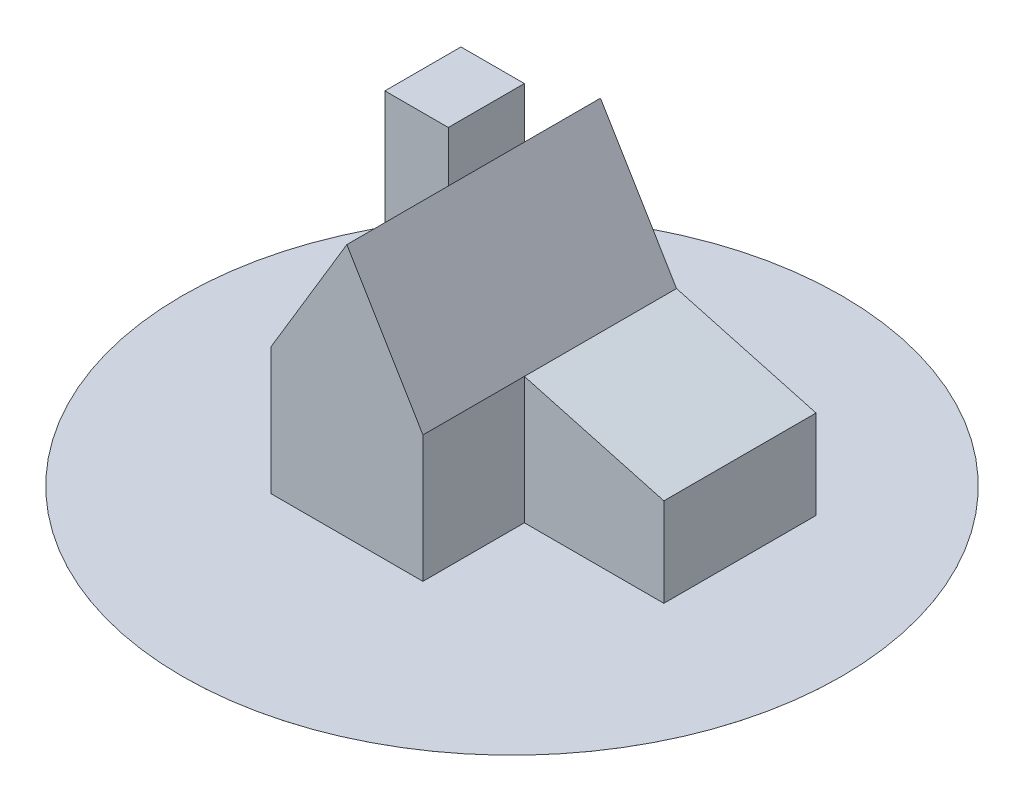
SolidWorks part; units mm, degrees
ref_plane "Front Plane" through (0, 0, 0) normal (0, 0, 1) x (1, 0, 0)
ref_plane "Top Plane" through (0, 0, 0) normal (0, 1, 0) x (1, 0, 0)
ref_plane "Right Plane" through (0, 0, 0) normal (1, 0, 0) x (0, 0, -1)
sketch "Sketch1" plane through (0, 0, 0) normal (0, 0, 1) x (1, 0, 0)
  line L0 (-60, 200) -> (0, 100)
  line L2 (-60, 200) -> (-120, 100)
  line L3 (-120, 100) -> (-120, 0)
  line L4 (-120, 0) -> (0, 0)
  line L5 (0, 100) -> (110, 70)
  line L6 (110, 70) -> (110, 0)
  line L7 (110, 0) -> (0, 0)
  dimension "D1" = 110
  dimension "D2" = 100
  dimension "D3" = 200
  dimension "D4" = 70
  dimension "D5" = 30
  dimension "D6" = 60
  dimension "D8" = 120
extrude "Extrude1" add sketch "Sketch1" along normal blind 200
sketch "Sketch2" plane through (0, 0, 0) normal (0, 1, 0) x (1, 0, 0)
  line L0 (0, -200) -> (0, 0) construction
  line L1 (110, -200) -> (0, -200)
  line L2 (110, -200) -> (110, -120)
  line L3 (110, -120) -> (0, -120)
  line L4 (0, -200) -> (0, -120)
  dimension "D1" = 80
extrude "Extrude2" cut sketch "Sketch2" along normal blind 200
sketch "Sketch3" plane through (0, 0, 0) normal (0, 1, 0) x (1, 0, 0)
  line L1 (-120, 0) -> (-170, 0)
  line L2 (-120, 0) -> (-120, -60)
  line L3 (-120, -60) -> (-170, -60)
  line L4 (-170, 0) -> (-170, -60)
  dimension "D1" = 50
  dimension "D2" = 60
extrude "Extrude3" add sketch "Sketch3" along normal blind 180
sketch "Sketch4" plane through (0, 0, 0) normal (0, 1, 0) x (1, 0, 0)
  line L0 (110, 0) -> (-170, -199.5199) construction
  circle A0 centre (-30, -99.76) radius 260
  dimension "D1" = 520
extrude "Extrude4" add sketch "Sketch4" along normal blind 0.01
